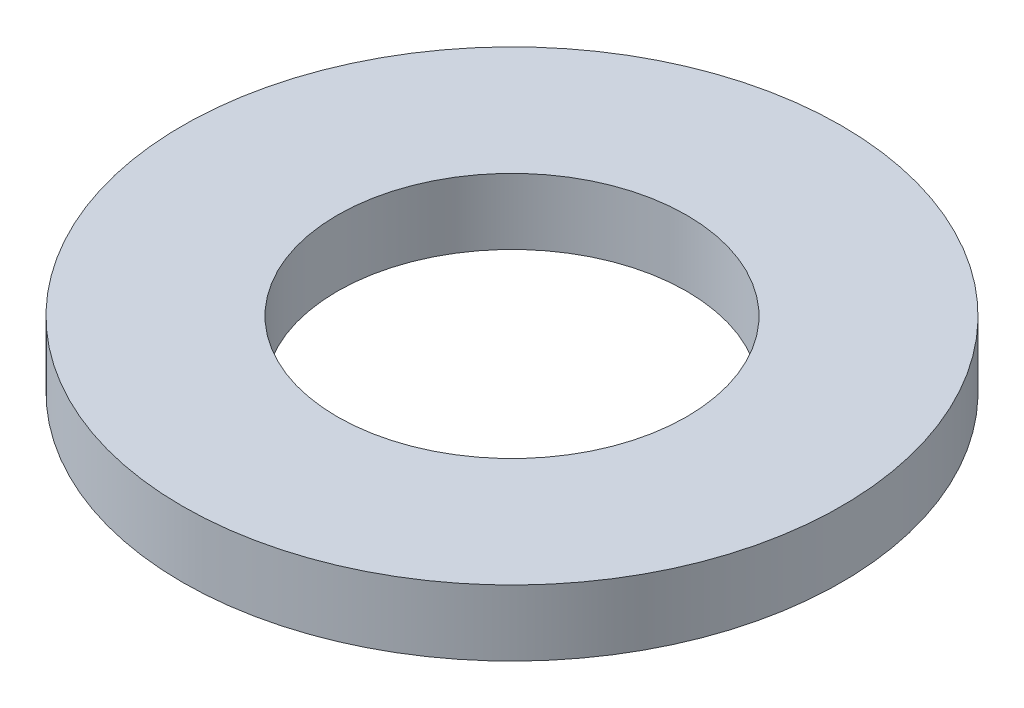
SolidWorks part; units mm, degrees
ref_plane "Front Plane" through (0, 0, 0) normal (0, 0, 1) x (1, 0, 0)
ref_plane "Top Plane" through (0, 0, 0) normal (0, 1, 0) x (1, 0, 0)
ref_plane "Right Plane" through (0, 0, 0) normal (1, 0, 0) x (0, 0, -1)
sketch "Sketch1" plane through (0, 0, 0) normal (0, 1, 0) x (1, 0, 0)
  circle A0 centre (0, 0) radius 2.65
  circle A1 centre (0, 0) radius 5
  dimension "D1" = 5.3
  dimension "D2" = 10
extrude "Boss-Extrude1" add sketch "Sketch1" along normal blind 1
